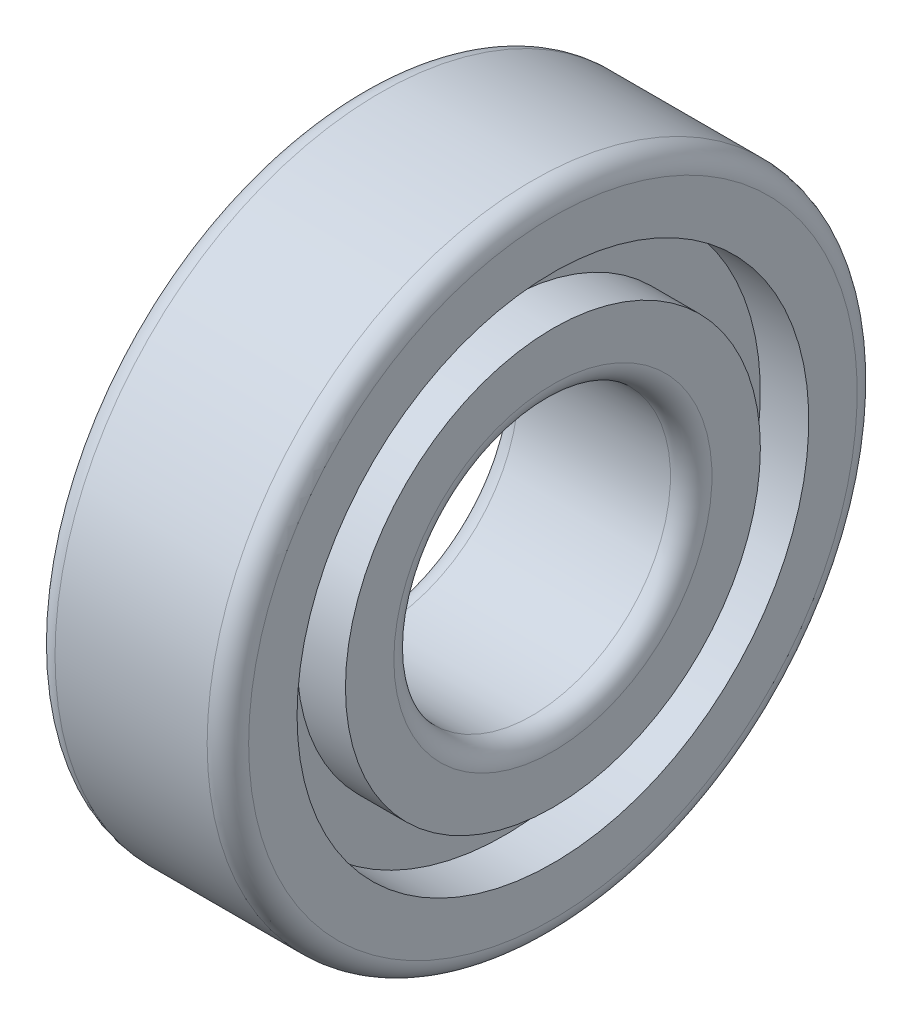
SolidWorks part; units mm, degrees
material "AISI 1020"
ref_plane "Спереди" through (0, 0, 0) normal (0, 0, 1) x (1, 0, 0)
ref_plane "Сверху" through (0, 0, 0) normal (0, 1, 0) x (1, 0, 0)
ref_plane "Справа" through (0, 0, 0) normal (1, 0, 0) x (0, 0, -1)
sketch "Эскиз1" plane through (0, 0, 0) normal (0, 0, 1) x (1, 0, 0)
  line L0 (5.5, 10) -> (-5.5, 10)
  line L1 (-7, 11.5) -> (-7, 15)
  line L2 (-7, 15) -> (-3.5, 15)
  line L3 (-3.5, 15) -> (-3.5, 18.5)
  line L4 (-3.5, 18.5) -> (-7, 18.5)
  line L5 (-7, 18.5) -> (-7, 22)
  line L6 (-5.5, 23.5) -> (5.5, 23.5)
  line L7 (-873.9917, 0) -> (42825.5954, 0) construction
  line L8 (0, -873.9917) -> (0, 42825.5954) construction
  line L9 (7, 18.5) -> (7, 22)
  line L10 (3.5, 18.5) -> (7, 18.5)
  line L11 (3.5, 15) -> (3.5, 18.5)
  line L12 (7, 15) -> (3.5, 15)
  line L13 (7, 11.5) -> (7, 15)
  arc A0 (-5.5, 10) -> (-7, 11.5) centre (-5.5, 11.5) cw
  arc A1 (-7, 22) -> (-5.5, 23.5) centre (-5.5, 22) cw
  arc A2 (7, 22) -> (5.5, 23.5) centre (5.5, 22) ccw
  arc A3 (5.5, 10) -> (7, 11.5) centre (5.5, 11.5) ccw
  point P25 (0, 23.5)
  point P29 (0, 10)
  dimension "D3" = 1.5
  dimension "B" = 14
  dimension "D1" = 20
  dimension "D2" = 47
  dimension "D4" = 3.5
revolve "Повернуть1" add sketch "Эскиз1" angle 360 about L7
equation "\"D4@Эскиз1\"=\"B@Эскиз1\"/4"
